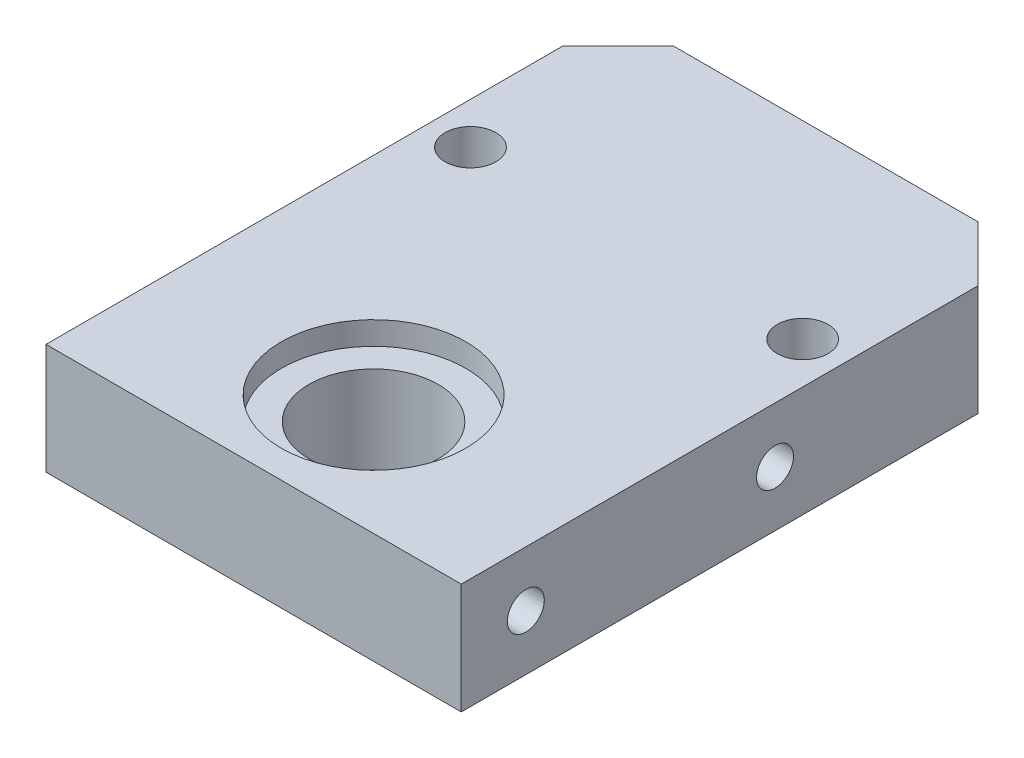
SolidWorks part; units mm, degrees
ref_plane "Front Plane" through (0, 0, 0) normal (0, 0, 1) x (1, 0, 0)
ref_plane "Top Plane" through (0, 0, 0) normal (0, 1, 0) x (1, 0, 0)
ref_plane "Right Plane" through (0, 0, 0) normal (1, 0, 0) x (0, 0, -1)
sketch "Sketch1" plane through (0, 0, 0) normal (0, 1, 0) x (1, 0, 0)
  line L1 (-22.5, 31) -> (22.5, 31)
  line L2 (-22.5, 31) -> (-22.5, -31)
  line L3 (-22.5, -31) -> (22.5, -31)
  line L4 (22.5, 31) -> (22.5, -31)
  line L5 (-22.5, 31) -> (22.5, -31) construction
  line L6 (-22.5, -31) -> (22.5, 31) construction
  point P0 (0, 0)
  dimension "D1" = 62
  dimension "D2" = 45
extrude "Boss-Extrude1" add sketch "Sketch1" along normal blind 12
sketch "Sketch2" plane through (0, 12, 0) normal (0, 1, 0) x (1, 0, 0)
  line L0 (-22.5, -31) -> (22.5, -31) construction
  line L1 (-22.5, 31) -> (-22.5, -31) construction
  line L2 (22.5, -31) -> (22.5, 31) construction
  circle A0 centre (0, -18) radius 7
  circle A1 centre (-18, 10.5) radius 2.75
  circle A2 centre (18, 10.5) radius 2.75
  dimension "D1" = 13
  dimension "D2" = 4.5
  dimension "D3" = 4.5
  dimension "D4" = 41.5
  dimension "D5" = 41.5
extrude "Cut-Extrude1" cut sketch "Sketch2" against normal blind 12
sketch "Sketch3" plane through (0, 12, 0) normal (0, 1, 0) x (1, 0, 0)
  circle A0 centre (0, -18) radius 10
extrude "Cut-Extrude2" cut sketch "Sketch3" against normal blind 2.5
sketch "Sketch4" plane through (-22.5, 0, 0) normal (-1, 0, 0) x (0, 0, 1)
  line L0 (31, 12) -> (31, 0) construction
  circle A0 centre (24, 6) radius 2
  circle A1 centre (-3, 6) radius 2
  dimension "D1" = 7
  dimension "D2" = 27
extrude "Cut-Extrude3" cut sketch "Sketch4" against normal blind 16
sketch "Sketch5" plane through (22.5, 0, 0) normal (1, 0, 0) x (0, 0, -1)
  line L0 (-31, 12) -> (-31, 0) construction
  circle A0 centre (-24, 6) radius 2
  circle A1 centre (3, 6) radius 2
  dimension "D1" = 7
  dimension "D2" = 27
extrude "Cut-Extrude4" cut sketch "Sketch5" against normal blind 16
chamfer "Chamfer1" distance 6 angle 45 2 edges at (-22.5, 6, -31) (22.5, 6, -31)
